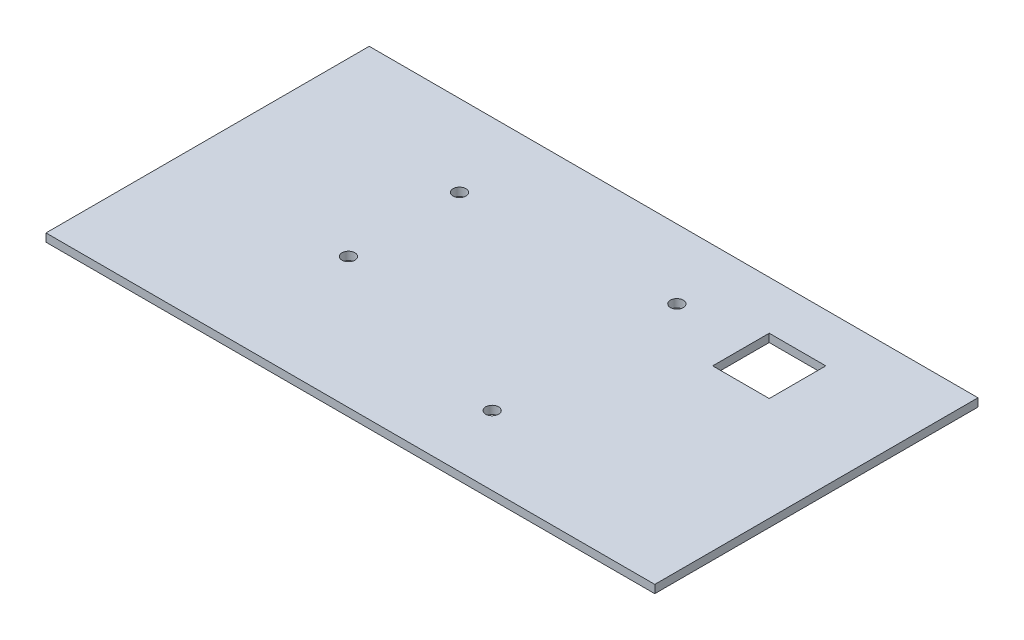
SolidWorks part; units mm, degrees
ref_plane "Front Plane" through (0, 0, 0) normal (0, 0, 1) x (1, 0, 0)
ref_plane "Top Plane" through (0, 0, 0) normal (0, 1, 0) x (1, 0, 0)
ref_plane "Right Plane" through (0, 0, 0) normal (1, 0, 0) x (0, 0, -1)
sketch "Sketch1" plane through (0, 0, 0) normal (0, 0, 1) x (1, 0, 0)
  line L1 (0, 0) -> (155, 0)
  line L2 (0, 0) -> (0, 110)
  line L3 (0, 110) -> (155, 110)
  line L4 (155, 0) -> (155, 110)
  dimension "D1" = 155
  dimension "D2" = 110
extrude "Boss-Extrude1" add sketch "Sketch1" along normal blind 80 contours L2 L1 L4 L3
sketch "Sketch2" plane through (0, 0, 80) normal (0, 0, 1) x (1, 0, 0)
  line L0 (0, 110) -> (2, 110) construction
  line L1 (0, 110) -> (155, 110) construction
  line L2 (0, 110) -> (0, 108) construction
  line L3 (0, 0) -> (0, 110) construction
  line L4 (155, 0) -> (155, 2) construction
  line L5 (155, 0) -> (155, 110) construction
  line L6 (155, 0) -> (153, 0) construction
  line L7 (0, 0) -> (155, 0) construction
  line L8 (0, 108) -> (2, 108) construction
  line L9 (2, 108) -> (2, 110) construction
  line L10 (155, 2) -> (153, 2) construction
  line L11 (153, 2) -> (153, 0) construction
  line L13 (153, 2) -> (2, 2)
  line L14 (153, 2) -> (153, 108)
  line L15 (153, 108) -> (2, 108)
  line L16 (2, 2) -> (2, 108)
  dimension "D1" = 2
  dimension "D2" = 2
  dimension "D3" = 2
  dimension "D4" = 2
extrude "Cut-Extrude1" cut sketch "Sketch2" against normal blind 78 contours L14 L13 L16 L15
sketch "Sketch3" plane through (0, 0, 2) normal (0, 0, 1) x (1, 0, 0)
  line L0 (2, 2) -> (6, 2) construction
  line L1 (153, 2) -> (2, 2) construction
  line L2 (153, 2) -> (149, 2) construction
  line L3 (2, 108) -> (6, 108) construction
  line L4 (153, 108) -> (2, 108) construction
  line L5 (2, 108) -> (2, 104.5) construction
  line L6 (2, 2) -> (2, 108) construction
  line L7 (149, 2) -> (149, 5.5) construction
  line L8 (2, 104.5) -> (6, 104.5) construction
  line L9 (6, 104.5) -> (6, 108) construction
  line L10 (6, 5.5) -> (10, 5.5) construction
  line L11 (6, 104.5) -> (149, 104.5)
  line L12 (6, 104.5) -> (6, 5.5)
  line L13 (6, 5.5) -> (149, 5.5)
  line L14 (149, 104.5) -> (149, 5.5)
  line L15 (10, 5.5) -> (10, 9.5) construction
  line L16 (149, 104.5) -> (145, 104.5) construction
  line L17 (145, 104.5) -> (145, 100.5) construction
  line L19 (10, 9.5) -> (145, 9.5)
  line L20 (10, 9.5) -> (10, 100.5)
  line L21 (10, 100.5) -> (145, 100.5)
  line L22 (145, 9.5) -> (145, 100.5)
  circle A0 centre (145, 100.5) radius 2.5
  circle A1 centre (145, 9.5) radius 2.5
  circle A2 centre (10, 9.5) radius 2.5
  circle A3 centre (10, 100.5) radius 2.5
  dimension "D10" = 5
  dimension "D11" = 5
  dimension "D12" = 5
  dimension "D13" = 5
  dimension "D1" = 4
  dimension "D2" = 3.5
  dimension "D3" = 4
  dimension "D4" = 4
  dimension "D5" = 3.5
  dimension "D6" = 4
  dimension "D7" = 4
  dimension "D8" = 4
  dimension "D9" = 4
extrude "Cut-Extrude2" cut sketch "Sketch3" against normal blind 2 contours A3 | A0 | A2 | A1
sketch "Sketch4" plane through (155, 0, 0) normal (1, 0, 0) x (0, 0, -1)
  line L1 (-53.75, 59.1) -> (-26.25, 59.1)
  line L3 (0, 55) -> (-80, 55) construction
  line L4 (0, 0) -> (0, 110) construction
  line L5 (-80, 0) -> (-80, 110) construction
  line L7 (-26.25, 105.9) -> (-26.25, 59.1)
  line L14 (-53.75, 105.9) -> (-26.25, 105.9)
  line L15 (-53.75, 105.9) -> (-53.75, 59.1)
  dimension "D1" = 46.8
  dimension "D2" = 27.5
sketch "Sketch7" plane through (0, 110, 0) normal (0, 1, 0) x (1, 0, 0)
  line L0 (0, -40) -> (155, -40) construction
  line L1 (0, -80) -> (0, 0) construction
  line L2 (155, -80) -> (155, 0) construction
  line L3 (77.5, 0) -> (77.5, -80) construction
  line L4 (0, 0) -> (155, 0) construction
  line L5 (0, -80) -> (155, -80) construction
  line L6 (110.52, -65.4) -> (95.28, -65.4) construction
  line L7 (44.48, -65.4) -> (110.52, -65.4)
  line L8 (44.48, -65.4) -> (44.48, -14.6)
  line L9 (44.48, -14.6) -> (110.52, -14.6)
  line L10 (110.52, -65.4) -> (110.52, -14.6)
  line L11 (44.48, -65.4) -> (110.52, -14.6) construction
  line L12 (44.48, -14.6) -> (110.52, -65.4) construction
  line L13 (95.28, -65.4) -> (95.28, -62.86) construction
  line L14 (110.52, -14.6) -> (95.28, -14.6) construction
  line L15 (44.48, -14.6) -> (44.48, -20.1445) construction
  line L16 (44.48, -65.4) -> (44.48, -47.62) construction
  line L17 (95.28, -14.6) -> (95.28, -17.14) construction
  line L18 (44.48, -65.4) -> (44.48, -19.68) construction
  circle A0 centre (44.48, -20.1445) radius 1.6
  circle A1 centre (95.28, -17.14) radius 1.6
  circle A2 centre (95.28, -62.86) radius 1.6
  circle A3 centre (44.48, -47.62) radius 1.6
  point P12 (77.5, -40)
  dimension "D9" = 3.2
  dimension "D10" = 3.2
  dimension "D11" = 3.2
  dimension "D12" = 3.2
  dimension "D1" = 66.04
  dimension "D2" = 50.8
  dimension "D3" = 15.24
  dimension "D4" = 2.54
  dimension "D5" = 15.24
  dimension "D6" = 2.54
  dimension "D7" = 17.78
  dimension "D8" = 45.72
extrude "Cut-Extrude7" cut sketch "Sketch7" against normal blind 2 contours A0 | A1 | A3 | A2
extrude "Cut-Extrude8" cut sketch "Sketch4" against normal blind 2
sketch "Sketch8" plane through (155, 0, 0) normal (1, 0, 0) x (0, 0, -1)
  line L0 (-80, 55) -> (0, 55) construction
  line L1 (-80, 0) -> (-80, 110) construction
  line L2 (0, 0) -> (0, 110) construction
  line L3 (0, 0) -> (-2, 0) construction
  line L4 (-80, 0) -> (0, 0) construction
  line L5 (-2, 0) -> (-2, 2) construction
  line L6 (-80, 0) -> (-78, 0) construction
  line L7 (-78, 0) -> (-78, 2) construction
  line L8 (-70, 2) -> (-70, 55)
  line L9 (-78, 2) -> (-74, 2)
  line L10 (-78, 2) -> (-78, 55)
  line L11 (-78, 55) -> (-74, 55)
  line L12 (-74, 2) -> (-74, 55)
  line L13 (-70, 2) -> (-66, 2)
  line L14 (-66, 2) -> (-66, 55)
  line L15 (-70, 55) -> (-66, 55)
  line L16 (-62, 2) -> (-62, 55)
  line L17 (-62, 2) -> (-58, 2)
  line L18 (-58, 2) -> (-58, 55)
  line L19 (-62, 55) -> (-58, 55)
  line L20 (-54, 2) -> (-54, 55)
  line L21 (-54, 2) -> (-50, 2)
  line L22 (-50, 2) -> (-50, 55)
  line L23 (-54, 55) -> (-50, 55)
  line L24 (-46, 2) -> (-46, 55)
  line L25 (-46, 2) -> (-42, 2)
  line L26 (-42, 2) -> (-42, 55)
  line L27 (-46, 55) -> (-42, 55)
  line L28 (-38, 2) -> (-38, 55)
  line L29 (-38, 2) -> (-34, 2)
  line L30 (-34, 2) -> (-34, 55)
  line L31 (-38, 55) -> (-34, 55)
  line L32 (-30, 2) -> (-30, 55)
  line L33 (-30, 2) -> (-26, 2)
  line L34 (-26, 2) -> (-26, 55)
  line L35 (-30, 55) -> (-26, 55)
  line L36 (-22, 2) -> (-22, 55)
  line L37 (-22, 2) -> (-18, 2)
  line L38 (-18, 2) -> (-18, 55)
  line L39 (-22, 55) -> (-18, 55)
  line L40 (-14, 2) -> (-14, 55)
  line L41 (-14, 2) -> (-10, 2)
  line L42 (-10, 2) -> (-10, 55)
  line L43 (-14, 55) -> (-10, 55)
  line L44 (-6, 2) -> (-6, 55)
  line L45 (-6, 2) -> (-2, 2)
  line L46 (-2, 2) -> (-2, 55)
  line L47 (-6, 55) -> (-2, 55)
  dimension "D1" = 2
  dimension "D2" = 2
  dimension "D3" = 2
  dimension "D4" = 2
  dimension "D5" = 4
extrude "Cut-Extrude9" cut sketch "Sketch8" against normal blind 2
sketch "Sketch9" plane through (0, 110, 0) normal (0, 1, 0) x (1, 0, 0)
  line L0 (0, -40) -> (155, -40) construction
  line L1 (0, -80) -> (0, 0) construction
  line L2 (155, -80) -> (155, 0) construction
  line L3 (155, -40) -> (120, -40) construction
  line L4 (120, -40) -> (120, -26) construction
  line L5 (120, -26) -> (113, -26) construction
  line L7 (113, -26) -> (127, -26)
  line L8 (113, -26) -> (113, -12)
  line L9 (113, -12) -> (127, -12)
  line L10 (127, -26) -> (127, -12)
  dimension "D1" = 35
  dimension "D2" = 14
  dimension "D3" = 7
  dimension "D4" = 14
  dimension "D5" = 14
extrude "Cut-Extrude10" cut sketch "Sketch9" against normal blind 2
sketch "Sketch10" plane through (0, 0, 0) normal (-1, 0, 0) x (0, 0, 1)
  line L0 (40, 110) -> (40, 0) construction
  line L1 (80, 110) -> (0, 110) construction
  line L2 (80, 0) -> (0, 0) construction
  line L3 (80, 55) -> (0, 55) construction
  line L4 (80, 0) -> (80, 110) construction
  line L5 (0, 0) -> (0, 110) construction
  line L6 (40, 55) -> (80, 55) construction
  line L7 (80, 55) -> (60, 55) construction
  line L8 (60, 55) -> (58, 55) construction
  line L9 (40, 95) -> (42.5, 95) construction
  line L10 (40, 15) -> (76, 15)
  line L11 (40, 15) -> (40, 95)
  line L12 (40, 95) -> (76, 95)
  line L13 (76, 15) -> (76, 95)
  line L14 (40, 15) -> (76, 95) construction
  line L15 (40, 95) -> (76, 15) construction
  line L16 (42.5, 95) -> (42.5, 92.5) construction
  line L17 (76, 15) -> (73.5, 15) construction
  line L18 (73.5, 15) -> (73.5, 17.5) construction
  line L19 (76, 15) -> (76, 19.4) construction
  line L20 (42.5, 92.5) -> (73.5, 92.5)
  line L21 (42.5, 92.5) -> (42.5, 17.5)
  line L22 (42.5, 17.5) -> (73.5, 17.5)
  line L23 (73.5, 92.5) -> (73.5, 17.5)
  line L24 (76, 19.4) -> (70.6, 19.4) construction
  line L25 (40, 95) -> (45.4, 95) construction
  line L26 (45.4, 95) -> (45.4, 90.6) construction
  line L28 (45.4, 90.6) -> (70.6, 90.6)
  line L29 (45.4, 90.6) -> (45.4, 19.4)
  line L30 (45.4, 19.4) -> (70.6, 19.4)
  line L31 (70.6, 90.6) -> (70.6, 19.4)
  circle A0 centre (73.5, 92.5) radius 1.25
  circle A1 centre (73.5, 17.5) radius 1.25
  circle A2 centre (42.5, 17.5) radius 1.25
  circle A3 centre (42.5, 92.5) radius 1.25
  dimension "D8" = 2.5
  dimension "D9" = 2.5
  dimension "D10" = 2.5
  dimension "D11" = 2.5
  dimension "D1" = 2
  dimension "D2" = 80
  dimension "D3" = 36
  dimension "D4" = 2.5
  dimension "D5" = 2.5
  dimension "D6" = 2.5
  dimension "D7" = 2.5
  dimension "D12" = 4.4
  dimension "D13" = 5.4
  dimension "D14" = 4.4
  dimension "D15" = 5.4
extrude "Cut-Extrude12" cut sketch "Sketch10" against normal blind 2 contours L31 L28 L29 L30 | A3 | A0 | A2 | A1
sketch "Sketch11" plane through (0, 0, 0) normal (-1, 0, 0) x (0, 0, 1)
  line L0 (40, 110) -> (40, 0) construction
  line L1 (80, 110) -> (0, 110) construction
  line L2 (80, 0) -> (0, 0) construction
  line L3 (20, 110) -> (20, 0) construction
  line L4 (0, 55) -> (0, 110) construction
  line L5 (0, 0) -> (0, 110) construction
  line L6 (40, 55) -> (0, 55) construction
  line L7 (0, 82.5) -> (40, 82.5) construction
  circle A0 centre (20, 55) radius 2.5
  circle A1 centre (20, 40) radius 2.5
  circle A2 centre (20, 25) radius 2.5
  circle A3 centre (20, 82.5) radius 4.5
  dimension "D1" = 5
  dimension "D3" = 9
  dimension "D2" = 3
extrude "Cut-Extrude13" cut sketch "Sketch11" against normal blind 2
sketch "Sketch12" plane through (0, 0, 80) normal (0, 0, 1) x (1, 0, 0)
  line L0 (2, 108) -> (2, 110) construction
  line L1 (0, 110) -> (155, 110) construction
  line L2 (153, 108) -> (153, 110) construction
  line L3 (0, 0) -> (155, 0) construction
  line L4 (2, 110) -> (0, 110)
  line L5 (2, 110) -> (2, 0)
  line L6 (2, 0) -> (0, 0)
  line L7 (0, 110) -> (0, 0)
  line L8 (155, 110) -> (152.6729, 110)
  line L9 (155, 110) -> (155, 0)
  line L10 (155, 0) -> (152.6729, 0)
  line L11 (152.6729, 110) -> (152.6729, 0)
  line L13 (152.6729, 0) -> (2, 0)
  line L14 (152.6729, 0) -> (152.6729, 108)
  line L15 (152.6729, 108) -> (2, 108)
  line L16 (2, 0) -> (2, 108)
  line M1 (2, 108) -> (153, 108)
  line M2 (153, 108) -> (153, 2)
  line M3 (153, 2) -> (2, 2)
  line M4 (2, 2) -> (2, 108)
  line M5 (155, 110) -> (0, 110)
  line M7 (0, 0) -> (155, 0)
  line M8 (155, 0) -> (155, 110)
extrude "Cut-Extrude14" cut sketch "Sketch12" against normal blind 80 contours L11 M1 M4 M3 | L11 M5 M1 M2 M3 M7 M8 | L5 L4 L7 L6
sketch "Sketch13" plane through (0, 0, 80) normal (0, 0, 1) x (1, 0, 0)
  line L1 (2, 2) -> (152.6729, 2)
  line L2 (2, 2) -> (2, 0)
  line L3 (2, 0) -> (152.6729, 0)
  line L4 (152.6729, 2) -> (152.6729, 0)
extrude "Cut-Extrude15" cut sketch "Sketch13" against normal blind 80
sketch "Sketch14" plane through (153, 0, 0) normal (1, 0, 0) x (0, 0, -1)
  line L1 (-2, 108) -> (0, 108)
  line L2 (-2, 108) -> (-2, 2)
  line L3 (-2, 2) -> (0, 2)
  line L4 (0, 108) -> (0, 2)
extrude "Cut-Extrude16" cut sketch "Sketch14" against normal blind 80
